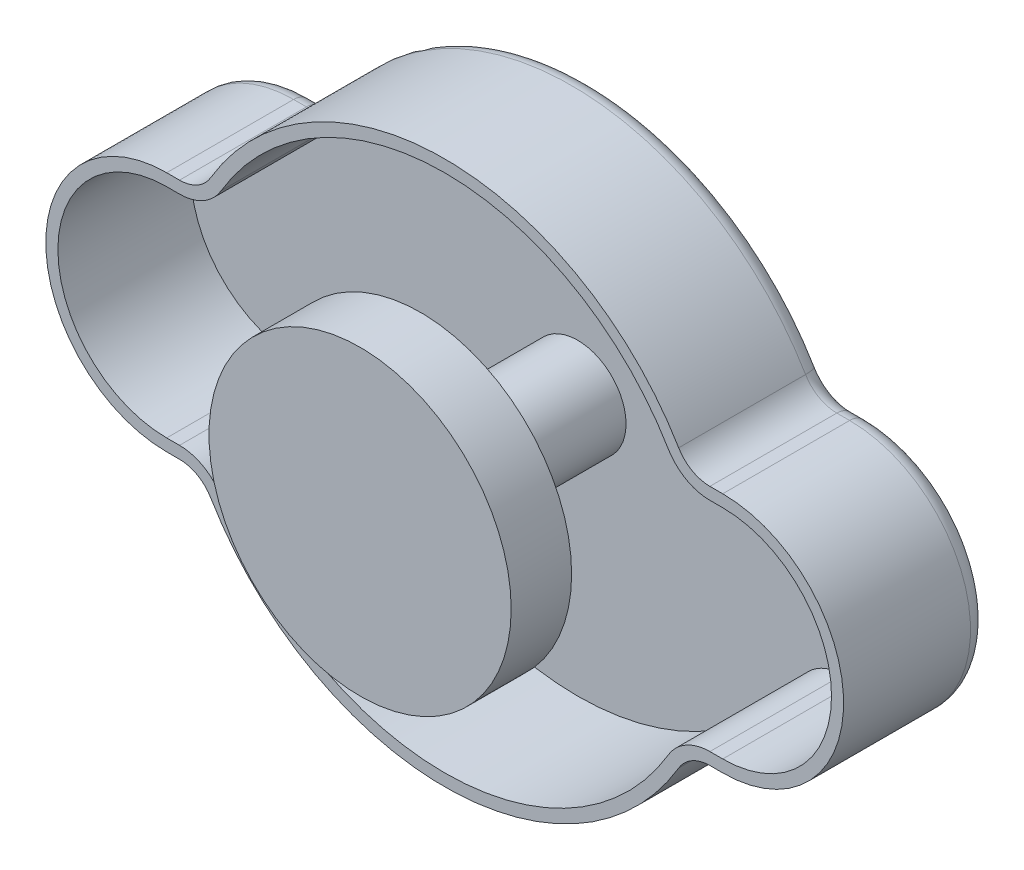
SolidWorks part; units mm, degrees
material "6061-T6 (SS)"
ref_plane "Płaszczyzna przednia" through (0, 0, 0) normal (0, 0, 1) x (1, 0, 0)
ref_plane "Płaszczyzna górna" through (0, 0, 0) normal (0, 1, 0) x (1, 0, 0)
ref_plane "Płaszczyzna prawa" through (0, 0, 0) normal (1, 0, 0) x (0, 0, -1)
sketch "Szkic1" plane through (0, 0, 0) normal (0, 0, 1) x (1, 0, 0)
  line L0 (-20.1556, 10) -> (-23, 10)
  line L2 (-23, -10) -> (-20.1556, -10)
  line L3 (-23, 0) -> (0, 0) construction
  line L4 (0, 0) -> (0, -14.1713) construction
  line L5 (23, -10) -> (20.1556, -10)
  line L7 (20.1556, 10) -> (23, 10)
  arc A0 (-20.1556, -10) -> (20.1556, -10) centre (0, 0) ccw
  arc A1 (-23, 10) -> (-23, -10) centre (-23, 0) ccw
  arc A2 (23, 10) -> (23, -10) centre (23, 0) cw
  arc A3 (20.1556, 10) -> (-20.1556, 10) centre (0, 0) ccw
  point P1 (-23, 11.5832)
  dimension "D1" = 45
  dimension "D3" = 46
  dimension "D2" = 20
extrude "Dodanie-wyciągnięcie1" add sketch "Szkic1" along normal blind 12
fillet "Zaokrąglenie1" radius 3 4 edges at (-20.1556, -10, 6) (20.1556, -10, 6) (20.1556, 10, 6) (-20.1556, 10, 6)
shell "Skorupa1" thickness 1
sketch "Szkic2" plane through (0, 0, 1) normal (0, 0, 1) x (1, 0, 0)
  circle A0 centre (0, 0) radius 4
  dimension "D1" = 8
extrude "Dodanie-wyciągnięcie2" add sketch "Szkic2" along normal blind 18
sketch "Szkic3" plane through (0, 0, 19) normal (0, 0, 1) x (1, 0, 0)
  circle A0 centre (0, 0) radius 12.5
  dimension "D1" = 25
extrude "Dodanie-wyciągnięcie3" add sketch "Szkic3" against normal blind 5 separate body
shell "Skorupa2" thickness 1
fillet "Zaokrąglenie2" radius 1.5 12 edges at (-20.4522, 10.3934, 0) (-22.4687, 10, 0) (-33, 0, 0) (-22.4687, -10, 0) (-20.4522, -10.3934, 0) (0, -22.5, 0) (20.4522, -10.3934, 0) (22.4687, -10, 0) (33, 0, 0) (22.4687, 10, 0) (20.4522, 10.3934, 0) (0, 22.5, 0)
